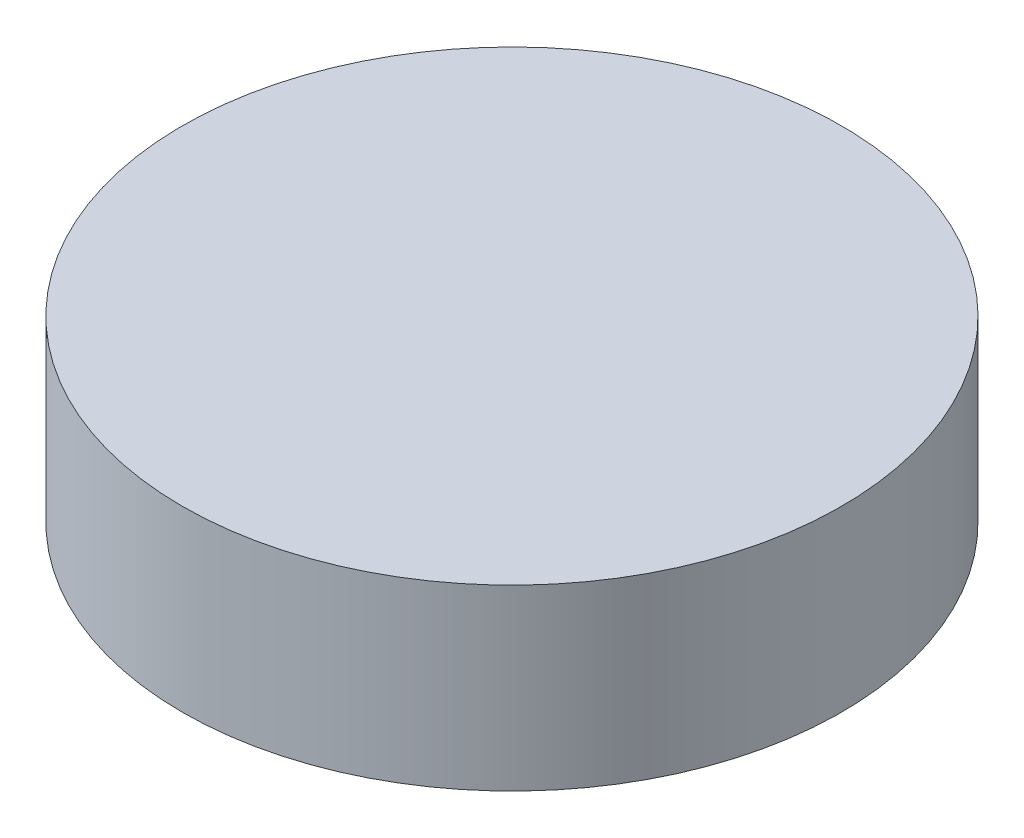
SolidWorks part; units mm, degrees
ref_plane "Front Plane" through (0, 0, 0) normal (0, 0, 1) x (1, 0, 0)
ref_plane "Top Plane" through (0, 0, 0) normal (0, 1, 0) x (1, 0, 0)
ref_plane "Right Plane" through (0, 0, 0) normal (1, 0, 0) x (0, 0, -1)
sketch "Sketch1" plane through (0, 0, 0) normal (0, 1, 0) x (1, 0, 0)
  circle A0 centre (0, 0) radius 170
  dimension "D1" = 340
extrude "Boss-Extrude1" add sketch "Sketch1" along normal blind 92
